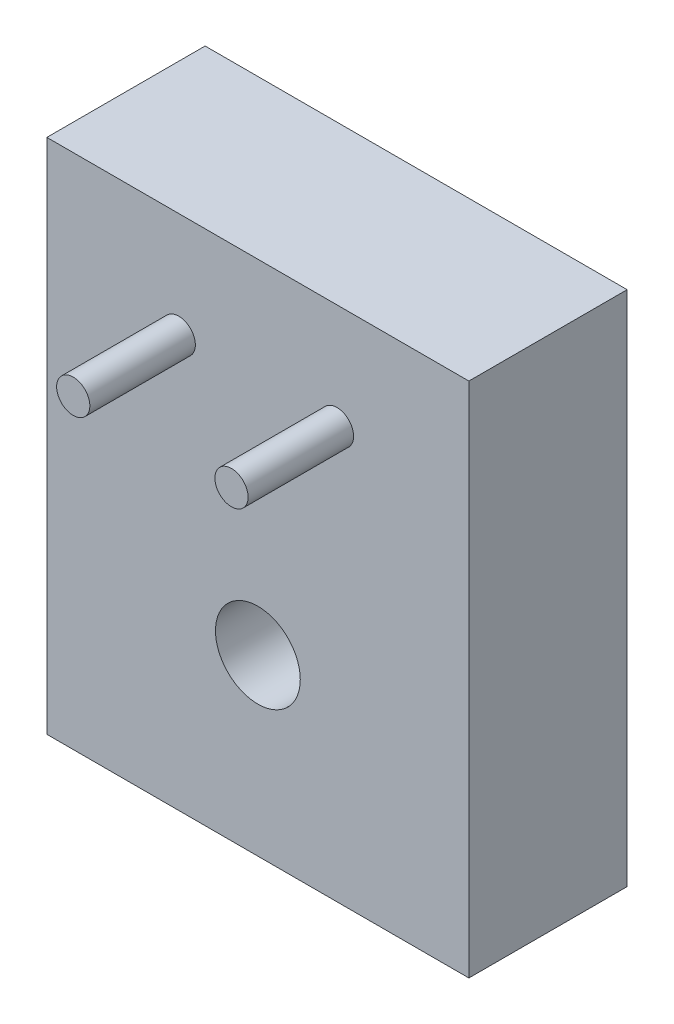
SolidWorks part; units mm, degrees
ref_plane "Front Plane" through (0, 0, 0) normal (0, 0, 1) x (1, 0, 0)
ref_plane "Top Plane" through (0, 0, 0) normal (0, 1, 0) x (1, 0, 0)
ref_plane "Right Plane" through (0, 0, 0) normal (1, 0, 0) x (0, 0, -1)
sketch "Sketch1" plane through (0, 0, 0) normal (0, 0, 1) x (1, 0, 0)
  line L0 (12.7, -31.115) -> (12.7, 0) construction
  line L1 (0, 0) -> (25.4, 0)
  line L2 (0, 0) -> (0, -31.115)
  line L3 (0, -31.115) -> (25.4, -31.115)
  line L4 (25.4, 0) -> (25.4, -31.115)
  line L6 (2.54, 0) -> (22.86, 0) construction
  line L7 (2.54, 0) -> (2.54, -10.16) construction
  line L8 (2.54, -10.16) -> (22.86, -10.16) construction
  line L9 (22.86, 0) -> (22.86, -10.16) construction
  line L10 (2.54, 0) -> (22.86, -10.16) construction
  line L11 (2.54, -10.16) -> (22.86, 0) construction
  circle A0 centre (12.7, -20.6375) radius 2.5527
  point P9 (12.7, -5.08)
  dimension "D2" = 5.1054
  dimension "D6" = 10.4775
  dimension "D1" = 25.4
  dimension "D3" = 10.4775
  dimension "D4" = 20.32
  dimension "D5" = 10.16
extrude "Boss-Extrude2" add sketch "Sketch1" along normal blind 9.525
sketch "Sketch2" plane through (0, 0, 9.525) normal (0, 0, 1) x (1, 0, 0)
  line L0 (12.7, 0) -> (12.7, -31.115) construction
  line L1 (0, -31.115) -> (25.4, -31.115) construction
  line L2 (25.4, 0) -> (0, 0) construction
  line L3 (7.9375, -6.35) -> (17.4625, -6.35) construction
  circle A0 centre (7.9375, -6.35) radius 1
  circle A1 centre (17.4625, -6.35) radius 1
  point P10 (12.7, -6.35)
  point P11 (12.7, -2.704)
  dimension "D1" = 2
  dimension "D2" = 9.525
  dimension "D3" = 6.35
extrude "Boss-Extrude3" add sketch "Sketch2" along normal blind 6.35 contours A0 | A1
